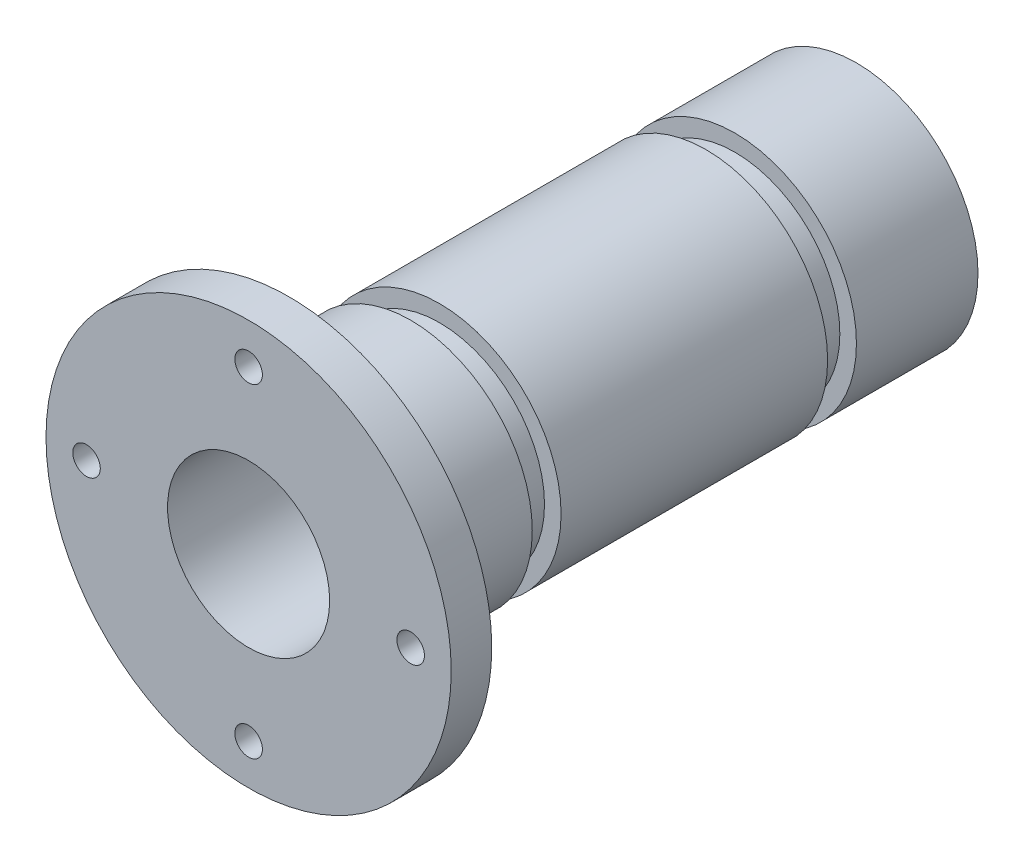
SolidWorks part; units mm, degrees
material "1060 Alloy"
ref_plane "Front Plane" through (0, 0, 0) normal (0, 0, 1) x (1, 0, 0)
ref_plane "Top Plane" through (0, 0, 0) normal (0, 1, 0) x (1, 0, 0)
ref_plane "Right Plane" through (0, 0, 0) normal (1, 0, 0) x (0, 0, -1)
sketch "Sketch1" plane through (0, 0, 0) normal (0, 0, 1) x (1, 0, 0)
  circle A0 centre (0, 0) radius 15
  circle A1 centre (0, 0) radius 10
  dimension "D1" = 30
  dimension "D2" = 20
extrude "Boss-Extrude1" add sketch "Sketch1" along normal mid plane 70
sketch "Sketch5" plane through (0, 0, 0) normal (1, 0, 0) x (0, 0, -1)
  line L0 (35, 15) -> (-35, 15) construction
  line L1 (-16.444, 15) -> (-20, 15)
  line L2 (-16.444, 15) -> (-16.444, 12.954)
  line L3 (-16.444, 12.954) -> (-20, 12.954)
  line L4 (-20, 15) -> (-20, 12.954)
  line L5 (-35, 15) -> (-35, -15) construction
  line L6 (0, 0) -> (-113.8802, 0) construction
  dimension "D1" = 3.556
  dimension "D2" = 12.954
  dimension "D3" = 15
revolve "Cut-Revolve1" cut sketch "Sketch5" angle 360 about L6
mirror "Mirror1" about plane through (0, 0, 0) normal (0, 0, 1) of "Cut-Revolve1"
sketch "Sketch6" plane through (0, 0, 35) normal (0, 0, 1) x (1, 0, 0)
  circle A0 centre (0, 0) radius 10
  circle A1 centre (0, 0) radius 25
  dimension "D1" = 20
  dimension "D2" = 50
extrude "Boss-Extrude2" add sketch "Sketch6" along normal blind 5
hole_wizard "M3 Clearance Hole1" positions "Sketch8" profile "Sketch9" hole size "M3" standard "ISO"
sketch "Sketch8" plane through (0, 0, 40) normal (0, 0, 1) x (1, 0, 0)
  point P0 (20, 0)
  dimension "D1" = 20
sketch "Sketch9" plane through (20, 0, 40) normal (1, 0, 0) x (0, -1, 0)
  line L0 (0, 0) -> (0, 18.5215)
  line L1 (0, 18.5215) -> (1.7, 17.5)
  line L2 (1.7, 17.5) -> (1.7, 0)
  line L5 (1.7, 0) -> (0, 0)
  line L10 (0, 18.5215) -> (-1.7, 17.5) construction
  line L11 (0, -6.35) -> (0, 107.95) construction
  dimension "Hole Dia." = 3.4
  dimension "Hole Depth" = 17.5
  dimension "Drill Angle" = 118
pattern_circular "CirPattern1" count 4 over 360 about axis through (0, 0, 0) along (0, 0, 1) of "M3 Clearance Hole1"
